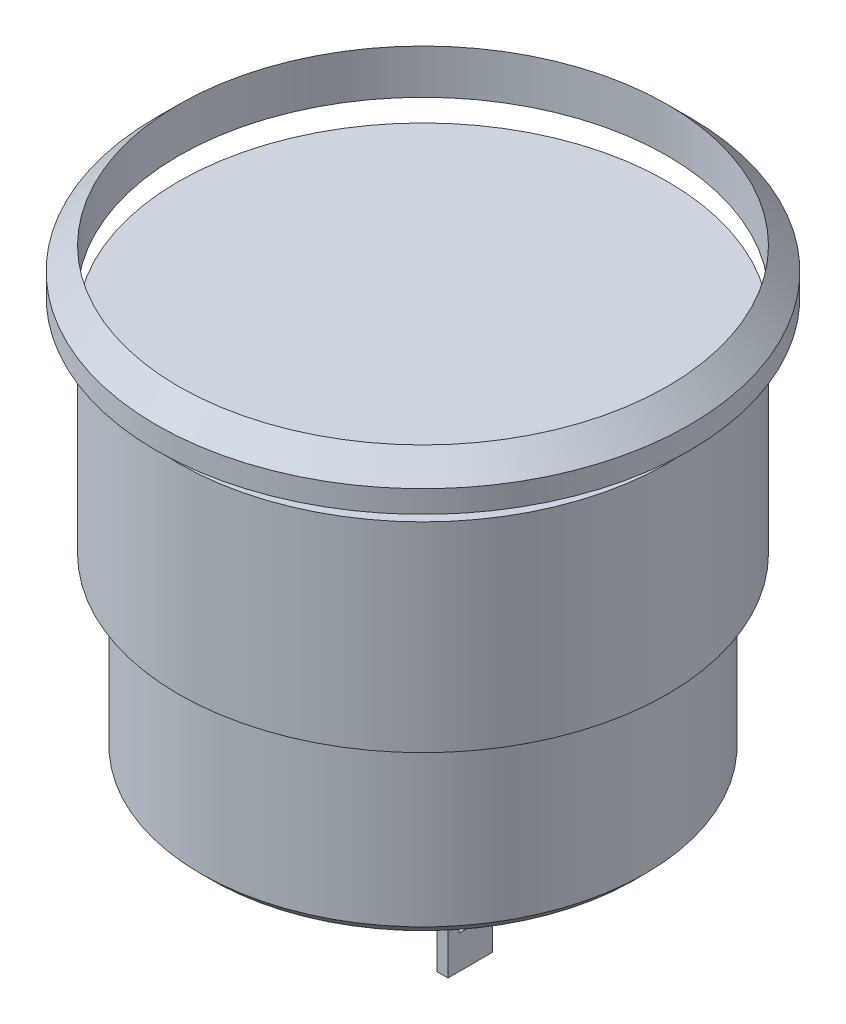
SolidWorks part; units mm, degrees
ref_plane "Front Plane" through (0, 0, 0) normal (0, 0, 1) x (1, 0, 0)
ref_plane "Top Plane" through (0, 0, 0) normal (0, 1, 0) x (1, 0, 0)
ref_plane "Right Plane" through (0, 0, 0) normal (1, 0, 0) x (0, 0, -1)
sketch "Sketch1" plane through (0, 0, 0) normal (0, 1, 0) x (1, 0, 0)
  circle A0 centre (0, 0) radius 12
  dimension "D1" = 24
extrude "Boss-Extrude1" add sketch "Sketch1" along normal blind 2
sketch "Sketch2" plane through (0, 0, 0) normal (0, -1, 0) x (1, 0, 0)
  circle A0 centre (0, 0) radius 11
  dimension "D1" = 22
extrude "Boss-Extrude2" add sketch "Sketch2" along normal blind 10
sketch "Sketch3" plane through (0, -10, 0) normal (0, -1, 0) x (1, 0, 0)
  circle A0 centre (0, 0) radius 10
  dimension "D1" = 20
extrude "Boss-Extrude3" add sketch "Sketch3" along normal blind 8
chamfer "Chamfer2" distance 1 angle 45 1 edges at (0, 2, 12)
chamfer "Chamfer3" distance 0.5 angle 45 1 edges at (0, -18, -10)
sketch "Sketch4" plane through (0, -18, 0) normal (0, -1, 0) x (1, 0, 0)
  line L0 (0, 0) -> (2.625, 0) construction
  line L1 (2.625, 0) -> (-2.625, 0) construction
  line L3 (2.625, 0) -> (3.125, 0)
  line L4 (2.625, 0) -> (2.625, 2)
  line L5 (2.625, 2) -> (3.125, 2)
  line L6 (3.125, 0) -> (3.125, 2)
  line L7 (-2.625, 0) -> (-3.125, 0)
  line L8 (-2.625, 0) -> (-2.625, 2)
  line L9 (-2.625, 2) -> (-3.125, 2)
  line L10 (-3.125, 0) -> (-3.125, 2)
extrude "Boss-Extrude4" add sketch "Sketch4" along normal blind 6
sketch "Sketch5" plane through (-3.125, 0, 0) normal (-1, 0, 0) x (0, 0, 1)
  line L0 (2, -24) -> (0, -24) construction
  line L1 (0.5, -21) -> (1.5, -21)
  line L2 (0.5, -21) -> (0.5, -22.5)
  line L3 (0.5, -22.5) -> (1.5, -22.5)
  line L4 (1.5, -21) -> (1.5, -22.5)
  line L5 (0.5, -21) -> (1.5, -22.5) construction
  line L6 (0.5, -22.5) -> (1.5, -21) construction
  line L7 (2, -24) -> (2, -18) construction
  line L8 (0, -24) -> (0, -18) construction
  point P0 (1, -21.75)
  dimension "D1" = 1.5
  dimension "D2" = 0.5
  dimension "D3" = 0.5
  dimension "D4" = 1.5
extrude "Cut-Extrude1" cut sketch "Sketch5" against normal through all
sketch "Sketch6" plane through (0, 2, 0) normal (0, 1, 0) x (1, 0, 0)
  circle A0 centre (0, 0) radius 11
  dimension "D1" = 22
sketch "Sketch7" plane through (0, -18, 0) normal (0, -1, 0) x (-1, 0, 0)
  text T0 "  3A125VAC\r\n1.5A250VAC" font "Century Gothic" height 0.7
extrude "Boss-Extrude6" add sketch "Sketch7" along normal blind 0.1
extrude "Cut-Extrude2" cut sketch "Sketch6" against normal blind 3
